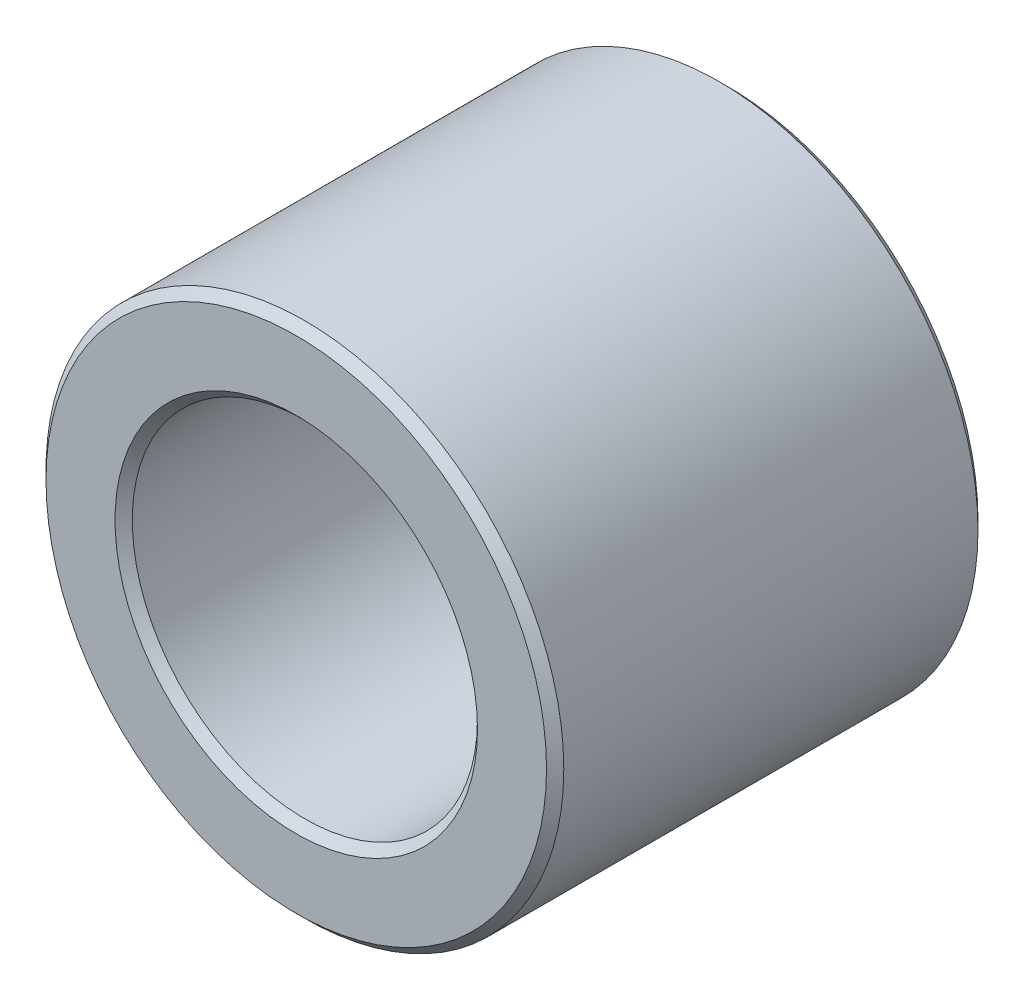
SolidWorks part; units mm, degrees
material "Laiton"
ref_plane "Plan de face" through (0, 0, 0) normal (0, 0, 1) x (1, 0, 0)
ref_plane "Plan de dessus" through (0, 0, 0) normal (0, 1, 0) x (1, 0, 0)
ref_plane "Plan de droite" through (0, 0, 0) normal (1, 0, 0) x (0, 0, -1)
sketch "Esquisse1" plane through (0, 0, 0) normal (0, 0, 1) x (1, 0, 0)
  circle A0 centre (0, 0) radius 6
  circle A1 centre (0, 0) radius 4
  dimension "D1" = 12
  dimension "D2" = 8
extrude "Boss.-Extru.1" add sketch "Esquisse1" along normal blind 10
chamfer "Chanfrein1" distance 0.2 angle 45 4 edges at (4, 0, 0) (6, 0, 0) (4, 0, 10) (6, 0, 10)
